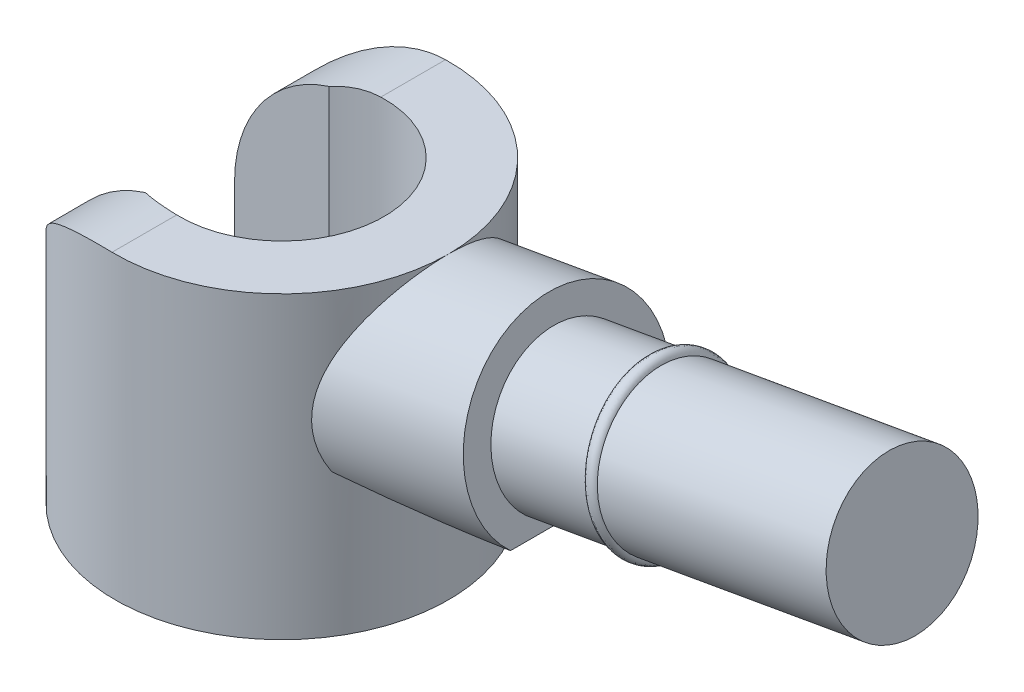
SolidWorks part; units mm, degrees
ref_plane "Front Plane" through (0, 0, 0) normal (0, 0, 1) x (1, 0, 0)
ref_plane "Top Plane" through (0, 0, 0) normal (0, 1, 0) x (1, 0, 0)
ref_plane "Right Plane" through (0, 0, 0) normal (1, 0, 0) x (0, 0, -1)
sketch "Sketch1" plane through (0, 0, 0) normal (0, 1, 0) x (1, 0, 0)
  circle A0 centre (0, 0) radius 2.45
  dimension "D1" = 4.9
extrude "Boss-Extrude1" add sketch "Sketch1" along normal blind 4.4
sketch "Sketch2" plane through (0, 4.4, 0) normal (0, 1, 0) x (1, 0, 0)
  circle A0 centre (0, 0) radius 1.5
  dimension "D1" = 3
sketch "Sketch4" plane through (0, 0, 0) normal (0, 1, 0) x (1, 0, 0)
  line L0 (-5.154, 1.35) -> (-0.6538, 1.35)
  line L1 (-0.6538, 1.35) -> (-0.6538, -1.35)
  line L2 (-0.6538, -1.35) -> (-5.154, -1.35)
  line L3 (-5.154, -1.35) -> (-5.154, 1.35)
  line L4 (-4.4135, 0) -> (4.4135, 0) construction
  circle A0 centre (0, 0) radius 1.5 construction
  dimension "D1" = 1.35
extrude "Cut-Extrude4" cut sketch "Sketch2" against normal through all
extrude "Cut-Extrude6" cut sketch "Sketch4" along normal through all
sketch "Sketch11" plane through (0, 0, 1.35) normal (0, 0, -1) x (-1, 0, 0)
  line L4 (2.0445, 0) -> (2.0445, 4.4) construction
  line L5 (0.6538, 4.4) -> (-1.5, 4.4) construction
  line L6 (2.0445, 2.4) -> (2.9118, 2.4)
  line L7 (2.9118, 2.4) -> (2.9118, 5.6132)
  line L8 (2.9118, 5.6132) -> (0.0445, 5.6132)
  line L9 (0.0445, 5.6132) -> (0.0445, 4.4)
  arc A0 (2.0445, 2.4) -> (0.0445, 4.4) centre (0.0445, 2.4) ccw
extrude "Cut-Extrude7" cut sketch "Sketch11" against normal through all and the other way through all
sketch "Sketch13" plane through (0, 0, 0) normal (0, 0, 1) x (1, 0, 0)
  line L0 (2.45, 4.4) -> (3.0571, 0.9567)
  line L1 (0, -2.695) -> (0, 2.695) construction
  dimension "D1" = 10
sketch "Sketch14" plane through (0, 0, 0) normal (1, 0, 0) x (0, 0, -1)
  line L0 (0, 4.4) -> (0, 0.9567) construction
  line L1 (-1.506, 3.8661) -> (1.8212, 3.8661)
  line L2 (-1.506, 3.8661) -> (-1.506, 1.0293)
  line L3 (-1.506, 1.0293) -> (1.8212, 1.0293)
  line L4 (1.8212, 3.8661) -> (1.8212, 1.0293)
  dimension "D1" = 1.8212
ref_plane "Plane1" through (0.6611, 0.1166, 0) normal (-0.9848, -0.1736, 0) x (0, 0, -1)
ref_plane "Plane2" through (3.1286, 0.5517, 0) normal (-0.9848, -0.1736, 0) x (0, 0, 1)
sketch "Sketch15" plane through (3.1286, 0.5517, 0) normal (-0.9848, -0.1736, 0) x (0, 0, 1)
  line L0 (0, 3.9077) -> (0, 0.4113) construction
  circle A0 centre (0, 2.4077) radius 1.5
  dimension "D1" = 3
extrude "Boss-Extrude2" add sketch "Sketch15" against normal blind 1.5 and the other way up to next
sketch "Sketch17" plane through (4.6058, 0.8121, 0) normal (0.9848, 0.1736, 0) x (0, 0, -1)
  line L0 (0, 3.9077) -> (0, 0.4113) construction
  circle A0 centre (0, 2.4077) radius 1.1
extrude "Boss-Extrude3" add sketch "Sketch17" along normal blind 5
ref_plane "Plane3" through (6.083, 1.0726, 0) normal (-0.9848, -0.1736, 0) x (0, 0, 1)
sketch "Sketch20" plane through (6.083, 1.0726, 0) normal (-0.9848, -0.1736, 0) x (0, 0, 1)
  line L0 (0, 3.9077) -> (0, 0.4113) construction
  circle A0 centre (0, 2.4077) radius 1.1 construction
  circle A1 centre (0, 2.4077) radius 1.1 construction
  ellipse E0 centre (0, 2.4077) end of major axis (0, 1.2577) minor radius 1.1
  dimension "D1" = 1.15
  dimension "D2" = 1.15
ref_plane "Plane6" through (4.5, 0, 0) normal (1, 0, 0) x (0, 0, -1)
sketch "Sketch22" plane through (4.5, 0, 0) normal (1, 0, 0) x (0, 0, -1)
  line L0 (-1.5927, 2.1) -> (1.8212, 2.1)
  line L1 (-1.5927, 2.1) -> (-1.5927, 1.3109)
  line L2 (-1.5927, 1.3109) -> (1.8212, 1.3109)
  line L3 (1.8212, 3.8661) -> (1.8212, 1.0293) construction
  line L4 (1.8212, 1.3109) -> (1.8212, 2.1)
  ellipse E0 centre (0, 3.1833) end of major axis (1.1, 3.1833) minor radius 1.0833 construction
extrude "Cut-Extrude8" cut sketch "Sketch22" against normal up to surface (2.8611 mm away)
sketch "Sketch23" plane through (0, 0, 0) normal (0, 0, 1) x (1, 0, 0)
  line L2 (8.9207, 5.1348) -> (3.9967, 4.2665) construction
  line L4 (5.6475, 3.5423) -> (6.5185, -1.3971) construction
  line L5 (5.4652, 4.5763) -> (5.8646, 2.3112) construction
  circle A0 centre (5.4739, 4.527) radius 0.1
  dimension "D1" = 0.2
sweep "Sweep1" add profiles "Sketch23" path "Sketch20"
equation "\"`1.5\"=1.52314"
